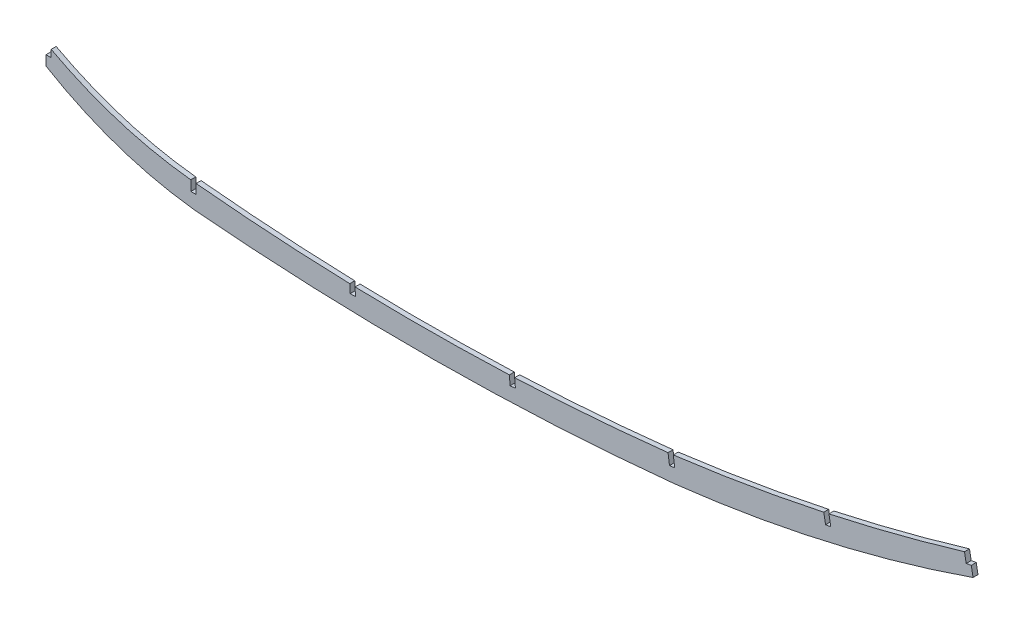
SolidWorks part; units mm, degrees
material "Plywood"
ref_plane "Front Plane" through (0, 0, 0) normal (0, 0, 1) x (1, 0, 0)
ref_plane "Top Plane" through (0, 0, 0) normal (0, 1, 0) x (1, 0, 0)
ref_plane "Right Plane" through (0, 0, 0) normal (1, 0, 0) x (0, 0, -1)
sketch "Sketch2" plane through (0, 0, 0) normal (0, 0, 1) x (1, 0, 0)
  line L0 (0, -94.4694) -> (0, -81.7694)
  line L1 (0, -94.4694) -> (93.98, -94.4694) construction
  line L2 (93.98, -126.4975) -> (93.98, -111.2575) construction
  line L3 (349.6407, -137.6462) -> (348.9613, -137.618) construction
  line L4 (349.6407, -137.6462) -> (354.8905, -137.8645) construction
  line L5 (93.98, -94.4694) -> (93.98, -126.4975) construction
  line L6 (400.2036, -124.7658) -> (400.2036, -94.4694) construction
  line L7 (590.8643, -81.3536) -> (588.5933, -68.8583)
  line L8 (0, 0) -> (672.417, 0) construction
  line L10 (93.98, -94.4694) -> (590.8643, -94.4694) construction
  line L11 (590.8643, -94.4694) -> (590.8643, -81.3536) construction
  line L12 (400.2036, -124.7658) -> (396.2207, -94.4694) construction
  arc A0 (0, -94.4694) -> (93.98, -126.4975) centre (121.7349, 108.8411) ccw
  arc A3 (93.98, -126.4975) -> (400.2036, -124.7658) centre (237.9716, 1487.1243) ccw
  arc A6 (400.2036, -124.7658) -> (590.8643, -81.3536) centre (300.4984, 753.5129) ccw
  arc A7 (93.98, -111.2575) -> (398.1841, -109.4039) centre (237.3586, 1321.3743) ccw
  arc A10 (0, -81.7694) -> (93.98, -111.2575) centre (118.1544, 130.2915) ccw
  arc A11 (398.1841, -109.4039) -> (588.5933, -68.8583) centre (254.6725, 1031.9221) ccw
  dimension "D3" = 236.9696
  dimension "D4" = 30.2963
  dimension "D5" = 400.2036
  dimension "D6" = 79.699
  dimension "D7" = 82.511
  dimension "D8" = 15.24
  dimension "D11" = 242.7557
  dimension "D14" = 1620.0336
  dimension "D15" = 883.92
  dimension "D16" = 15.494
  dimension "D18" = 1150.3133
  dimension "D1" = 12.7
  dimension "D2" = 81.7694
  dimension "D9" = 32.028
  dimension "D10" = 93.98
  dimension "D12" = 13.1158
  dimension "D13" = 496.8843
  dimension "D17" = 12.7
extrude "Boss-Extrude1" add sketch "Sketch2" against normal blind 3.175
sketch "Sketch3" plane through (0, 0, 0) normal (0, 0, 1) x (1, 0, 0)
  line L0 (0, 0) -> (0, -81.8237) construction
  line L1 (0, 0) -> (93.98, 0) construction
  line L2 (93.98, 0) -> (93.98, -117.6075) construction
  line L4 (0, -81.8237) -> (0, -88.1813)
  line L5 (0, -88.1813) -> (3.302, -88.1813)
  line L6 (3.302, -81.8237) -> (3.302, -88.1813)
  line L8 (0, -81.8237) -> (0, -80.8493)
  line L9 (0, -80.8493) -> (3.302, -80.8493)
  line L10 (3.302, -80.8493) -> (3.302, -81.8237)
  line L12 (92.2909, -117.5313) -> (95.6691, -117.5313)
  line L13 (92.2909, -117.5313) -> (92.2909, -108.4147)
  line L14 (92.2909, -108.4147) -> (95.6691, -108.4147)
  line L15 (95.6691, -117.5313) -> (95.6691, -108.4147)
  line L30 (195.5404, -123.1566) -> (190.3839, 0) construction
  line L31 (93.98, 0) -> (612.4013, 0) construction
  line L32 (574.4157, 0) -> (588.1634, -75.3909) construction
  line L33 (193.8496, -123.1511) -> (197.2249, -123.0098)
  line L34 (193.8496, -123.1511) -> (193.5511, -116.0212)
  line L35 (197.2249, -123.0098) -> (196.9263, -115.8799)
  line L36 (193.5511, -116.0212) -> (196.9263, -115.8799)
  line L37 (397.3751, -116.2998) -> (400.7239, -115.855)
  line L38 (397.3751, -116.2998) -> (395.8625, -104.9127)
  line L39 (286.9301, 0) -> (297.4996, -122.788) construction
  line L40 (295.8233, -123.0088) -> (299.189, -122.7191)
  line L41 (295.8233, -123.0088) -> (295.1616, -115.3225)
  line L42 (299.189, -122.7191) -> (298.5274, -115.0328)
  line L43 (295.1616, -115.3225) -> (298.5274, -115.0328)
  line L44 (383.6307, 0) -> (399.0395, -116.0018) construction
  line L45 (400.7239, -115.855) -> (399.2113, -104.4679)
  line L46 (395.8625, -104.9127) -> (399.2113, -104.4679)
  line L48 (586.5153, -75.7689) -> (589.8387, -75.1629)
  line L49 (480.4996, 0) -> (498.5238, -98.843) construction
  line L50 (496.8758, -99.221) -> (500.1992, -98.615)
  line L51 (496.8758, -99.221) -> (495.4086, -91.1748)
  line L52 (500.1992, -98.615) -> (498.732, -90.5688)
  line L53 (495.4086, -91.1748) -> (498.732, -90.5688)
  line L56 (586.5153, -75.7689) -> (585.2098, -68.6095)
  line L57 (589.8387, -75.1629) -> (588.5332, -68.0035)
  line L58 (585.2098, -68.6095) -> (588.5332, -68.0035)
  point P14 (93.98, -108.4147)
  point P25 (195.2387, -115.9505)
  point P28 (297.5062, -122.864)
  point P31 (399.0495, -116.0774)
  point P39 (498.5375, -98.918)
  point P51 (588.177, -75.4659)
  dimension "D1" = 81.8237
  dimension "D2" = 6.3576
  dimension "D3" = 3.302
  dimension "D4" = 93.98
  dimension "D5" = 117.6075
  dimension "D6" = 3.3782
  dimension "D7" = 0.0762
  dimension "D8" = 92.398
  dimension "D9" = 0.0762
  dimension "D10" = 3.3782
  dimension "D11" = 190.3839
  dimension "D12" = 123.2645
  dimension "D13" = 94.92
  dimension "D14" = 96.5461
  dimension "D15" = 123.2421
  dimension "D16" = 0.0762
  dimension "D17" = 3.3782
  dimension "D18" = 96.7007
  dimension "D19" = 97.566
  dimension "D20" = 117.0207
  dimension "D21" = 0.0762
  dimension "D22" = 3.3782
  dimension "D23" = 96.8689
  dimension "D24" = 100.334
  dimension "D25" = 100.473
  dimension "D26" = 3.3782
  dimension "D27" = 0.0762
  dimension "D28" = 93.9161
  dimension "D29" = 76.6341
  dimension "D30" = 100.334
  dimension "D31" = 0.0762
  dimension "D32" = 3.3782
extrude "Cut-Extrude2" cut sketch "Sketch3" against normal through all from surface at 0 starting at face at (270.5939, -104.1002, 0)
